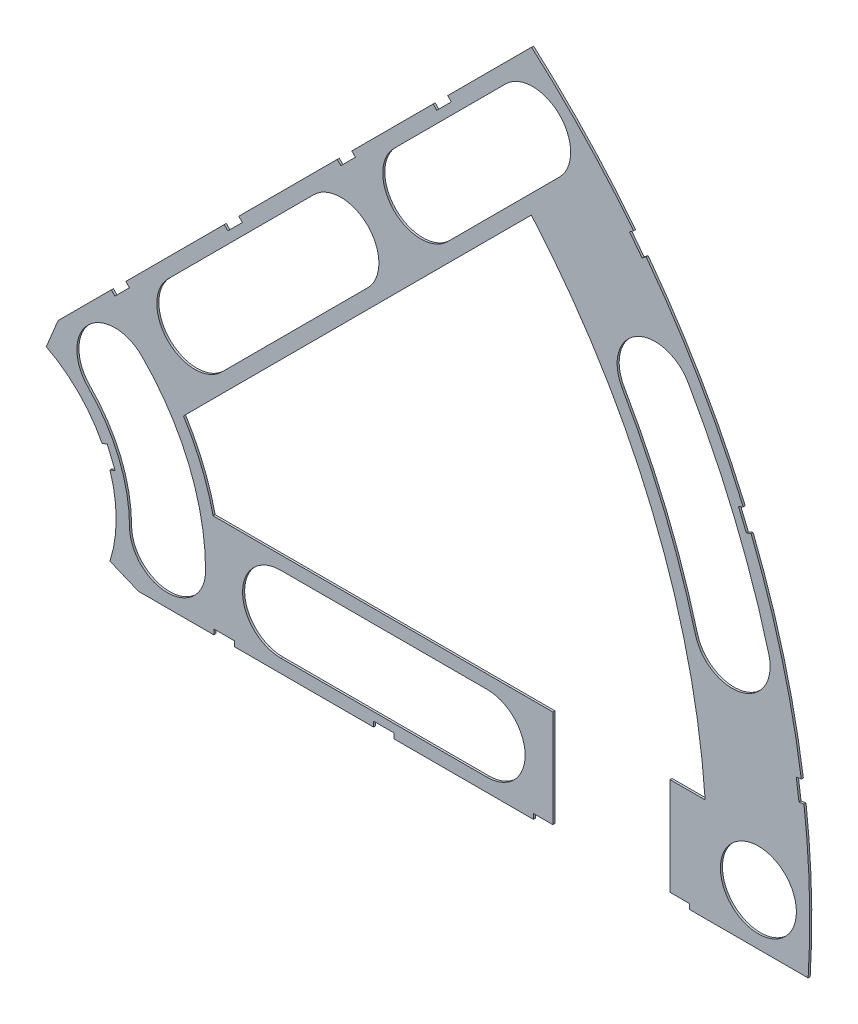
SolidWorks part; units mm, degrees
material "PTFE (general)"
ref_plane "Front Plane" through (0, 0, 0) normal (0, 0, 1) x (1, 0, 0)
ref_plane "Top Plane" through (0, 0, 0) normal (0, 1, 0) x (1, 0, 0)
ref_plane "Right Plane" through (0, 0, 0) normal (1, 0, 0) x (0, 0, -1)
sketch "Sketch1" plane through (0, 0, 0) normal (0, 0, 1) x (1, 0, 0)
  line L0 (0, 0) -> (320.3893, 0) construction
  line L1 (0, 0) -> (155.5285, 155.5285) construction
  line L2 (67.2115, 76.1917) -> (8.6967, 17.6769)
  line L3 (8.6967, 17.6769) -> (7.229, 14.1336)
  line L4 (101.4014, -6.35) -> (18.6489, -6.35)
  line L5 (15.1056, -4.8823) -> (18.6489, -6.35)
  line L6 (88.6729, 6.35) -> (27.8605, 6.35)
  line L9 (67.1914, 58.2111) -> (24.1905, 15.2102)
  line L10 (0, 0) -> (40.4486, 97.6516) construction
  line L11 (0, 0) -> (123.4567, -51.1374) construction
  line L18 (8.6967, 17.6769) -> (13.294, 8.6183) construction
  line L19 (18.6489, -6.35) -> (15.4943, 3.3063) construction
  line L20 (27.8605, 6.35) -> (27.7442, 6.7059) construction
  line L21 (24.1905, 15.2102) -> (24.3599, 14.8764) construction
  arc A0 (7.229, 14.1336) -> (15.1056, -4.8823) centre (0, 0) cw
  arc A1 (67.2115, 76.1917) -> (101.4014, -6.35) centre (0, 0) cw
  arc A2 (24.1905, 15.2102) -> (27.8605, 6.35) centre (0, 0) cw
  arc A3 (67.1914, 58.2111) -> (88.6729, 6.35) centre (0, 0) cw
  arc A8 (13.294, 8.6183) -> (15.4943, 3.3063) centre (0, 0) cw construction
  arc A9 (24.3599, 14.8764) -> (27.7442, 6.7059) centre (0, 0) cw construction
  dimension "D1" = 45
  dimension "D3" = 6.35
  dimension "D4" = 15.875
  dimension "D7" = 22.5
  dimension "D8" = 101.6
  dimension "D11" = 12.7
  dimension "D12" = 12.7
  dimension "D2" = 6.35
  dimension "D5" = 67.5
  dimension "D9" = 1.27
  dimension "D10" = 1.27
  dimension "D6" = 12.7
extrude "Boss-Extrude1" add sketch "Sketch1" along normal blind 0.254
sketch "Sketch2" plane through (0, 0, 0.254) normal (0, 0, 1) x (1, 0, 0)
  line L0 (0, 0) -> (101.6, 0) construction
  line L1 (0, 0) -> (71.842, 71.842) construction
  line L3 (0, 0) -> (22.225, 0) construction
  line L4 (0, 0) -> (15.7154, 15.7154) construction
  line L5 (0, 0) -> (95.25, 0) construction
  line L6 (0, 0) -> (92.0044, 24.6525) construction
  arc A0 (101.4014, -6.35) -> (67.2115, 76.1917) centre (0, 0) ccw construction
  circle A1 centre (22.225, 0) radius 4.699
  arc A2 (15.1056, -4.8823) -> (7.229, 14.1336) centre (0, 0) ccw construction
  circle A3 centre (36.195, 0) radius 4.699
  circle A4 centre (61.722, 0) radius 4.699
  circle A5 centre (75.692, 0) radius 4.699
  circle A6 centre (95.25, 0) radius 4.699
  circle A7 centre (15.7154, 15.7154) radius 4.699
  circle A8 centre (25.5937, 25.5937) radius 4.699
  circle A9 centre (43.644, 43.644) radius 4.699
  circle A10 centre (53.5223, 53.5223) radius 4.699
  circle A11 centre (92.0044, 24.6525) radius 4.699
  circle A12 centre (82.4889, 47.625) radius 4.699
  circle A13 centre (67.3519, 67.3519) radius 4.699
  dimension "D3" = 9.398
  dimension "D1" = 45
  dimension "D2" = 6.35
  dimension "D4" = 6.35
  dimension "D5" = 13.97
  dimension "D7" = 13.97
  dimension "D8" = 19.558
  dimension "D9" = 45
  dimension "D10" = 15
  dimension "D11" = 25.527
  dimension "D6" = 2
extrude "Cut-Extrude1" cut sketch "Sketch2" against normal through all
sketch "Sketch3" plane through (0, 0, 0.254) normal (0, 0, 1) x (1, 0, 0)
  line L0 (15.2664, 24.2467) -> (17.0625, 26.0427)
  line L1 (15.2664, 24.2467) -> (15.7154, 23.7977)
  line L2 (17.0625, 26.0427) -> (17.5115, 25.5937)
  line L3 (15.7154, 23.7977) -> (17.5115, 25.5937)
  line L4 (67.2115, 76.1917) -> (8.6967, 17.6769) construction
  line L5 (44.9911, 53.9713) -> (43.195, 52.1753)
  line L6 (44.9911, 53.9713) -> (45.4401, 53.5223)
  line L7 (43.195, 52.1753) -> (43.644, 51.7263)
  line L8 (45.4401, 53.5223) -> (43.644, 51.7263)
  line L9 (27.94, -6.35) -> (30.48, -6.35)
  line L10 (27.94, -6.35) -> (27.94, -5.715)
  line L11 (30.48, -6.35) -> (30.48, -5.715)
  line L12 (27.94, -5.715) -> (30.48, -5.715)
  line L13 (18.6489, -6.35) -> (101.4014, -6.35) construction
  line L14 (67.437, -6.35) -> (69.977, -6.35)
  line L15 (67.437, -6.35) -> (67.437, -5.715)
  line L16 (69.977, -6.35) -> (69.977, -5.715)
  line L17 (67.437, -5.715) -> (69.977, -5.715)
  line L18 (29.2307, 38.211) -> (31.0268, 40.007)
  line L19 (29.2307, 38.211) -> (29.6797, 37.762)
  line L20 (31.0268, 40.007) -> (31.4758, 39.558)
  line L21 (29.6797, 37.762) -> (31.4758, 39.558)
  line L22 (56.845, 65.8253) -> (55.049, 64.0292)
  line L23 (56.845, 65.8253) -> (57.294, 65.3763)
  line L24 (55.049, 64.0292) -> (55.498, 63.5802)
  line L25 (57.294, 65.3763) -> (55.498, 63.5802)
  line L26 (47.6885, -6.35) -> (50.2285, -6.35)
  line L27 (47.6885, -6.35) -> (47.6885, -5.715)
  line L28 (50.2285, -6.35) -> (50.2285, -5.715)
  line L29 (47.6885, -5.715) -> (50.2285, -5.715)
  line L30 (84.201, -6.35) -> (86.741, -6.35)
  line L31 (84.201, -6.35) -> (84.201, -5.715)
  line L32 (86.741, -6.35) -> (86.741, -5.715)
  line L33 (84.201, -5.715) -> (86.741, -5.715)
  line L34 (0, 0) -> (100.7308, 13.2615) construction
  line L35 (0, 0) -> (93.8662, 38.8806) construction
  line L36 (0, 0) -> (80.6047, 61.8502) construction
  line L37 (0, 0) -> (101.6, 0) construction
  line L38 (99.9355, 14.4377) -> (100.267, 11.9194)
  line L39 (99.9355, 14.4377) -> (101.1946, 14.6035)
  line L40 (100.267, 11.9194) -> (101.5261, 12.0852)
  line L41 (101.1946, 14.6035) -> (101.5261, 12.0852)
  line L42 (99.9355, 14.4377) -> (101.5261, 12.0852) construction
  line L43 (100.267, 11.9194) -> (101.1946, 14.6035) construction
  line L44 (93.7655, 37.4643) -> (94.9388, 37.9503)
  line L45 (93.7655, 37.4643) -> (92.7935, 39.811)
  line L46 (94.9388, 37.9503) -> (93.9668, 40.297)
  line L47 (92.7935, 39.811) -> (93.9668, 40.297)
  line L48 (93.7655, 37.4643) -> (93.9668, 40.297) construction
  line L49 (94.9388, 37.9503) -> (92.7935, 39.811) construction
  line L50 (79.3278, 62.4712) -> (80.874, 60.456)
  line L51 (79.3278, 62.4712) -> (80.3354, 63.2443)
  line L52 (80.874, 60.456) -> (81.8816, 61.2292)
  line L53 (80.3354, 63.2443) -> (81.8816, 61.2292)
  line L54 (79.3278, 62.4712) -> (81.8816, 61.2292) construction
  line L55 (80.874, 60.456) -> (80.3354, 63.2443) construction
  line L56 (13.5939, 7.0054) -> (14.5659, 4.6588)
  line L57 (13.5939, 7.0054) -> (14.7672, 7.4914)
  line L58 (14.5659, 4.6588) -> (15.7393, 5.1448)
  line L59 (14.7672, 7.4914) -> (15.7393, 5.1448)
  line L60 (13.5939, 7.0054) -> (15.7393, 5.1448) construction
  line L61 (14.5659, 4.6588) -> (14.7672, 7.4914) construction
  circle A0 centre (15.7154, 15.7154) radius 4.699 construction
  circle A1 centre (43.644, 43.644) radius 4.699 construction
  circle A2 centre (22.225, 0) radius 4.699 construction
  circle A3 centre (61.722, 0) radius 4.699 construction
  arc A4 (101.4014, -6.35) -> (67.2115, 76.1917) centre (0, 0) ccw construction
  arc A9 (15.1056, -4.8823) -> (7.229, 14.1336) centre (0, 0) ccw construction
  circle A10 centre (36.195, 0) radius 4.699 construction
  circle A11 centre (75.692, 0) radius 4.699 construction
  circle A12 centre (25.5937, 25.5937) radius 4.699 construction
  circle A13 centre (53.5223, 53.5223) radius 4.699 construction
  point P75 (14.6666, 6.0751)
  dimension "D2" = 5.715
  dimension "D3" = 2.54
  dimension "D6" = 5.715
  dimension "D8" = 0.635
  dimension "D9" = 5.715
  dimension "D12" = 5.715
  dimension "D4" = 7.5
  dimension "D5" = 22.5
  dimension "D7" = 37.5
  dimension "D10" = 90
  dimension "D11" = 1.27
  dimension "D14" = 0.635
  dimension "D15" = 90
  dimension "D18" = 0.635
  dimension "D19" = 90
  dimension "D22" = 0.635
  dimension "D20" = 1.27
  dimension "D17" = 0.635
  dimension "D13" = 11.4935
  dimension "D16" = 8.509
  dimension "D21" = 11.4935
  dimension "D23" = 8.509
extrude "Cut-Extrude2" cut sketch "Sketch3" against normal through all
sketch "Sketch5" plane through (0, 0, 0.254) normal (0, 0, 1) x (1, 0, 0)
  line L0 (27.8605, 6.35) -> (88.6729, 6.35) construction
  line L1 (69.85, -7.62) -> (84.328, -7.62)
  line L2 (69.85, -7.62) -> (69.85, 7.62)
  line L4 (69.85, 7.62) -> (84.328, 7.62)
  line L5 (84.328, -7.62) -> (84.328, 7.62)
  line L8 (67.437, -5.715) -> (67.437, -6.35) construction
  line L9 (86.741, -6.35) -> (86.741, -5.715) construction
  line L10 (69.977, -6.35) -> (84.201, -6.35) construction
  dimension "D1" = 1.27
  dimension "D2" = 2.413
  dimension "D3" = 2.413
  dimension "D4" = 1.27
sketch "Sketch6" plane through (0, 0, 0.254) normal (0, 0, 1) x (1, 0, 0)
  line L0 (0, 0) -> (101.6, 0) construction
  line L1 (0, 0) -> (71.842, 71.842) construction
  line L2 (0, 0) -> (87.9882, 50.8) construction
  line L3 (0, 0) -> (98.1381, 26.296) construction
  line L4 (25.5937, 25.5937) -> (43.644, 43.644) construction
  line L5 (22.271, 28.9164) -> (40.3213, 46.9667)
  line L6 (28.9164, 22.271) -> (46.9667, 40.3213)
  line L7 (53.5223, 53.5223) -> (67.3519, 67.3519) construction
  line L8 (50.1996, 56.845) -> (64.0292, 70.6746)
  line L9 (56.845, 50.1996) -> (70.6746, 64.0292)
  line L10 (61.722, 0) -> (36.195, 0) construction
  line L11 (61.722, -4.699) -> (36.195, -4.699)
  line L12 (61.722, 4.699) -> (36.195, 4.699)
  arc A0 (79.8253, 62.8529) -> (67.2115, 76.1917) centre (0, 0) ccw construction
  arc A1 (15.7154, 15.7154) -> (22.225, 0) centre (0, 0) cw construction
  arc A2 (26.924, 0) -> (19.0381, 19.0381) centre (0, 0) ccw
  arc A3 (17.526, 0) -> (12.3928, 12.3928) centre (0, 0) ccw
  arc A4 (17.526, 0) -> (26.924, 0) centre (22.225, 0) ccw
  arc A5 (101.4014, -6.35) -> (100.8887, 12.0013) centre (0, 0) ccw construction
  arc A6 (19.0381, 19.0381) -> (12.3928, 12.3928) centre (15.7154, 15.7154) ccw
  arc A7 (93.3728, 40.0509) -> (81.3715, 60.8378) centre (0, 0) ccw construction
  arc A8 (100.5572, 14.5196) -> (94.3448, 37.7043) centre (0, 0) ccw construction
  arc A9 (82.4889, 47.625) -> (92.0044, 24.6525) centre (0, 0) cw construction
  arc A10 (96.5433, 25.8687) -> (86.5584, 49.9745) centre (0, 0) ccw
  arc A11 (87.4655, 23.4363) -> (78.4195, 45.2755) centre (0, 0) ccw
  arc A12 (87.4655, 23.4363) -> (96.5433, 25.8687) centre (92.0044, 24.6525) ccw
  arc A13 (86.5584, 49.9745) -> (78.4195, 45.2755) centre (82.4889, 47.625) ccw
  arc A14 (22.271, 28.9164) -> (28.9164, 22.271) centre (25.5937, 25.5937) ccw
  arc A15 (46.9667, 40.3213) -> (40.3213, 46.9667) centre (43.644, 43.644) ccw
  arc A16 (50.1996, 56.845) -> (56.845, 50.1996) centre (53.5223, 53.5223) ccw
  arc A17 (70.6746, 64.0292) -> (64.0292, 70.6746) centre (67.3519, 67.3519) ccw
  arc A18 (61.722, -4.699) -> (61.722, 4.699) centre (61.722, 0) ccw
  arc A19 (36.195, 4.699) -> (36.195, -4.699) centre (36.195, 0) ccw
  circle A20 centre (67.3519, 67.3519) radius 4.699 construction
  circle A21 centre (43.644, 43.644) radius 4.699 construction
  point P8 (20.5332, 8.5051)
  point P12 (87.9995, 36.4506)
  point P43 (34.6189, 34.6189)
  point P48 (60.4371, 60.4371)
  point P59 (48.9585, 0)
  dimension "D2" = 9.398
  dimension "D5" = 9.398
  dimension "D1" = 45
  dimension "D3" = 9.398
  dimension "D4" = 9.398
extrude "Cut-Extrude4" cut sketch "Sketch6" against normal through all
extrude "Cut-Extrude5" cut sketch "Sketch5" against normal through all
equation "\"cSep\"= 1.005"
equation "\"D11@Sketch2\"=\"cSep\""
equation "\"cSep2\"= \"D8@Sketch2\""
equation "\"D13@Sketch3\"=\"cSep\"/2-.05"
equation "\"D16@Sketch3\"=\"cSep2\"/2-.05"
equation "\"D21@Sketch3\"=\"cSep\"/2-.05"
equation "\"D23@Sketch3\"=\"cSep2\"/2-.05"
